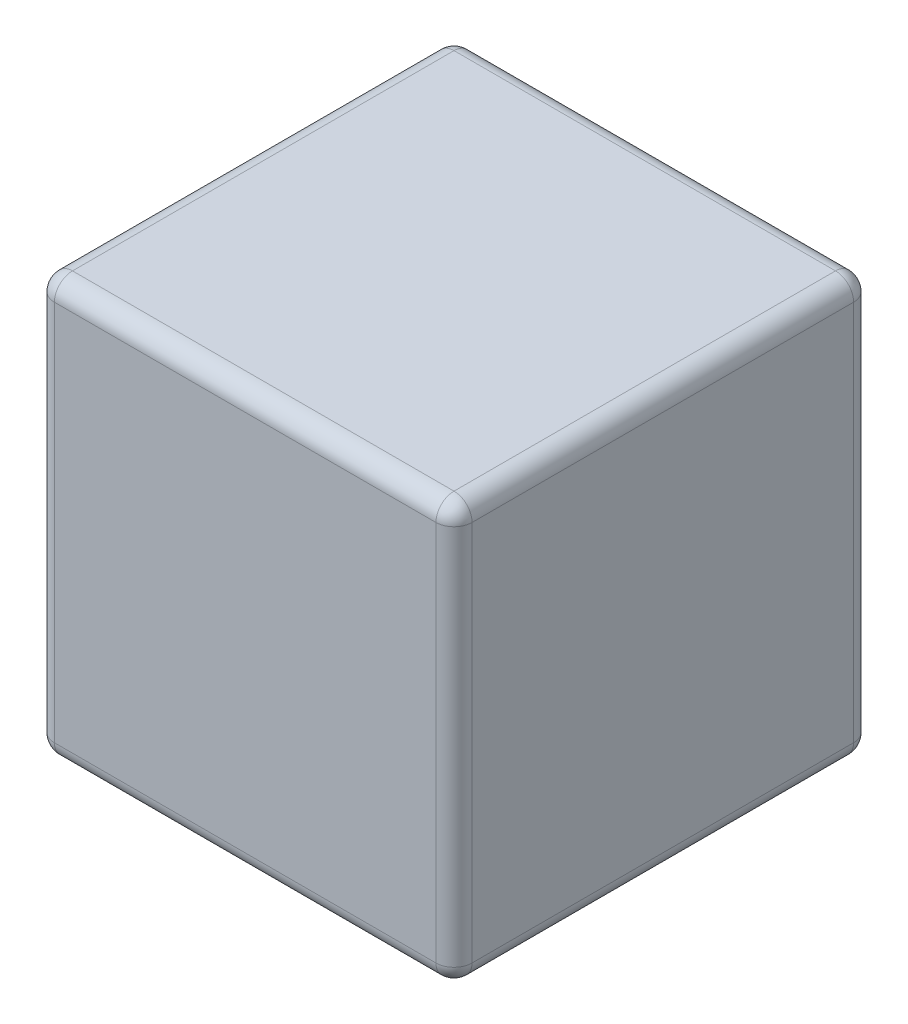
SolidWorks part; units mm, degrees
ref_plane "Front" through (0, 0, 0) normal (0, 0, 1) x (1, 0, 0)
ref_plane "Top" through (0, 0, 0) normal (0, 1, 0) x (1, 0, 0)
ref_plane "Right" through (0, 0, 0) normal (1, 0, 0) x (0, 0, -1)
sketch "Sketch1" plane through (0, 0, 0) normal (0, 0, 1) x (1, 0, 0)
  line L1 (-5.775, -5.775) -> (5.775, -5.775)
  line L2 (-5.775, -5.775) -> (-5.775, 5.775)
  line L3 (-5.775, 5.775) -> (5.775, 5.775)
  line L4 (5.775, -5.775) -> (5.775, 5.775)
  line L5 (-5.775, -5.775) -> (5.775, 5.775) construction
  line L6 (-5.775, 5.775) -> (5.775, -5.775) construction
  point P0 (0, 0)
  dimension "D1" = 11.55
  dimension "D2" = 11.55
extrude "Boss-Extrude1" add sketch "Sketch1" along normal blind 11.55
fillet "Fillet1" radius 0.5 12 edges at (0, -5.775, 0) (-5.775, -5.775, 5.775) (-5.775, 0, 0) (-5.775, 5.775, 5.775) (0, 5.775, 0) (0, -5.775, 11.55) (-5.775, 0, 11.55) (0, 5.775, 11.55) (5.775, -5.775, 5.775) (5.775, 0, 11.55) (5.775, 5.775, 5.775) (5.775, 0, 0)
